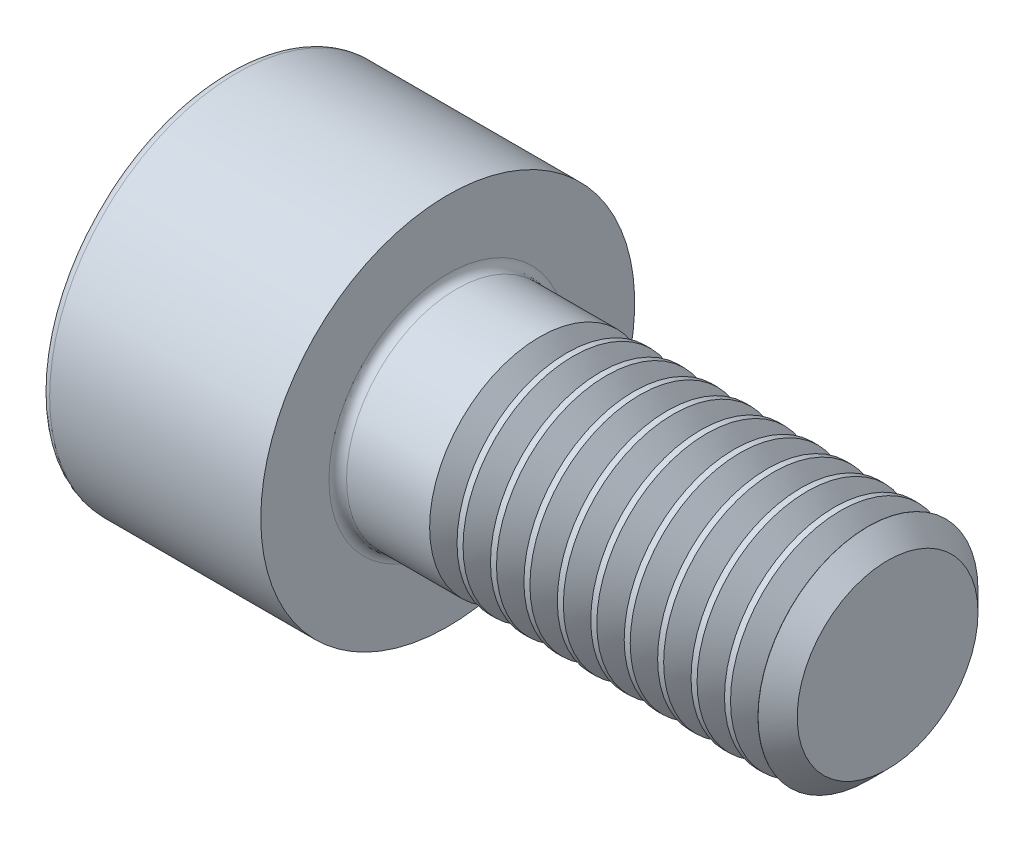
SolidWorks part; units mm, degrees
ref_plane "Front" through (0, 0, 0) normal (0, 0, 1) x (1, 0, 0)
ref_plane "Top" through (0, 0, 0) normal (0, 1, 0) x (1, 0, 0)
ref_plane "Right" through (0, 0, 0) normal (1, 0, 0) x (0, 0, -1)
ref_plane "Plane1" through (0, 0, 0) normal (0, 0, -1) x (-1, 0, 0)
sketch "Sketch1" plane through (0, 0, 0) normal (0, 0, -1) x (-1, 0, 0)
  line L0 (3.7906, 4.4808) -> (3.7906, 0.2308)
  line L1 (3.7906, 0.2308) -> (8.7906, 0.2308)
  line L2 (8.7906, 0.2308) -> (8.7906, 4.4808)
  line L3 (8.7906, 4.4808) -> (3.7906, 4.4808)
  line L4 (3.7906, 0.2308) -> (8.7906, 0.2308) construction
revolve "Revolve1" add sketch "Sketch1" angle 360 about L4
sketch "Sketch2" plane through (-3.7906, 0, 0) normal (1, 0, 0) x (0, 0, -1)
  circle A0 centre (0, 0.2308) radius 2.5
extrude "Boss-Extrude1" add sketch "Sketch2" along normal blind 2.0884
sketch "Sketch3" plane through (-1.7022, 0, 0) normal (1, 0, 0) x (0, 0, -1)
  circle A0 centre (0, 0.2308) radius 2.5
extrude "Boss-Extrude2" add sketch "Sketch3" along normal blind 0.3116 draft 55
sketch "Sketch4" plane through (-1.3906, 0, 0) normal (1, 0, 0) x (0, 0, -1)
  circle A0 centre (0, 0.2308) radius 2.055
extrude "Boss-Extrude3" add sketch "Sketch4" along normal blind 0.3116 draft 55 draft outward yes
sketch "Sketch5" plane through (-1.079, 0, 0) normal (1, 0, 0) x (0, 0, -1)
  circle A0 centre (0, 0.2308) radius 2.5
extrude "Boss-Extrude4" add sketch "Sketch5" along normal blind 0.1368
sketch "Sketch6" plane through (-0.9422, 0, 0) normal (1, 0, 0) x (0, 0, -1)
  circle A0 centre (0, 0.2308) radius 2.5
extrude "Boss-Extrude5" add sketch "Sketch6" along normal blind 0.3116 draft 55
sketch "Sketch7" plane through (-0.6306, 0, 0) normal (1, 0, 0) x (0, 0, -1)
  circle A0 centre (0, 0.2308) radius 2.055
extrude "Boss-Extrude6" add sketch "Sketch7" along normal blind 0.3116 draft 55 draft outward yes
sketch "Sketch8" plane through (-0.319, 0, 0) normal (1, 0, 0) x (0, 0, -1)
  circle A0 centre (0, 0.2308) radius 2.5
extrude "Boss-Extrude7" add sketch "Sketch8" along normal blind 0.1368
sketch "Sketch9" plane through (-0.1822, 0, 0) normal (1, 0, 0) x (0, 0, -1)
  circle A0 centre (0, 0.2308) radius 2.5
extrude "Boss-Extrude8" add sketch "Sketch9" along normal blind 0.3116 draft 55
sketch "Sketch10" plane through (0.1294, 0, 0) normal (1, 0, 0) x (0, 0, -1)
  circle A0 centre (0, 0.2308) radius 2.055
extrude "Boss-Extrude9" add sketch "Sketch10" along normal blind 0.3116 draft 55 draft outward yes
sketch "Sketch11" plane through (0.441, 0, 0) normal (1, 0, 0) x (0, 0, -1)
  circle A0 centre (0, 0.2308) radius 2.5
extrude "Boss-Extrude10" add sketch "Sketch11" along normal blind 0.1368
sketch "Sketch12" plane through (0.5778, 0, 0) normal (1, 0, 0) x (0, 0, -1)
  circle A0 centre (0, 0.2308) radius 2.5
extrude "Boss-Extrude11" add sketch "Sketch12" along normal blind 0.3116 draft 55
sketch "Sketch13" plane through (0.8894, 0, 0) normal (1, 0, 0) x (0, 0, -1)
  circle A0 centre (0, 0.2308) radius 2.055
extrude "Boss-Extrude12" add sketch "Sketch13" along normal blind 0.3116 draft 55 draft outward yes
sketch "Sketch14" plane through (1.201, 0, 0) normal (1, 0, 0) x (0, 0, -1)
  circle A0 centre (0, 0.2308) radius 2.5
extrude "Boss-Extrude13" add sketch "Sketch14" along normal blind 0.1368
sketch "Sketch15" plane through (1.3378, 0, 0) normal (1, 0, 0) x (0, 0, -1)
  circle A0 centre (0, 0.2308) radius 2.5
extrude "Boss-Extrude14" add sketch "Sketch15" along normal blind 0.3116 draft 55
sketch "Sketch16" plane through (1.6494, 0, 0) normal (1, 0, 0) x (0, 0, -1)
  circle A0 centre (0, 0.2308) radius 2.055
extrude "Boss-Extrude15" add sketch "Sketch16" along normal blind 0.3116 draft 55 draft outward yes
sketch "Sketch17" plane through (1.961, 0, 0) normal (1, 0, 0) x (0, 0, -1)
  circle A0 centre (0, 0.2308) radius 2.5
extrude "Boss-Extrude16" add sketch "Sketch17" along normal blind 0.1368
sketch "Sketch18" plane through (2.0978, 0, 0) normal (1, 0, 0) x (0, 0, -1)
  circle A0 centre (0, 0.2308) radius 2.5
extrude "Boss-Extrude17" add sketch "Sketch18" along normal blind 0.3116 draft 55
sketch "Sketch19" plane through (2.4094, 0, 0) normal (1, 0, 0) x (0, 0, -1)
  circle A0 centre (0, 0.2308) radius 2.055
extrude "Boss-Extrude18" add sketch "Sketch19" along normal blind 0.3116 draft 55 draft outward yes
sketch "Sketch20" plane through (2.721, 0, 0) normal (1, 0, 0) x (0, 0, -1)
  circle A0 centre (0, 0.2308) radius 2.5
extrude "Boss-Extrude19" add sketch "Sketch20" along normal blind 0.1368
sketch "Sketch21" plane through (2.8578, 0, 0) normal (1, 0, 0) x (0, 0, -1)
  circle A0 centre (0, 0.2308) radius 2.5
extrude "Boss-Extrude20" add sketch "Sketch21" along normal blind 0.3116 draft 55
sketch "Sketch22" plane through (3.1694, 0, 0) normal (1, 0, 0) x (0, 0, -1)
  circle A0 centre (0, 0.2308) radius 2.055
extrude "Boss-Extrude21" add sketch "Sketch22" along normal blind 0.3116 draft 55 draft outward yes
sketch "Sketch23" plane through (3.481, 0, 0) normal (1, 0, 0) x (0, 0, -1)
  circle A0 centre (0, 0.2308) radius 2.5
extrude "Boss-Extrude22" add sketch "Sketch23" along normal blind 0.1368
sketch "Sketch24" plane through (3.6178, 0, 0) normal (1, 0, 0) x (0, 0, -1)
  circle A0 centre (0, 0.2308) radius 2.5
extrude "Boss-Extrude23" add sketch "Sketch24" along normal blind 0.3116 draft 55
sketch "Sketch25" plane through (3.9294, 0, 0) normal (1, 0, 0) x (0, 0, -1)
  circle A0 centre (0, 0.2308) radius 2.055
extrude "Boss-Extrude24" add sketch "Sketch25" along normal blind 0.3116 draft 55 draft outward yes
sketch "Sketch26" plane through (4.241, 0, 0) normal (1, 0, 0) x (0, 0, -1)
  circle A0 centre (0, 0.2308) radius 2.5
extrude "Boss-Extrude25" add sketch "Sketch26" along normal blind 0.1368
sketch "Sketch27" plane through (4.3778, 0, 0) normal (1, 0, 0) x (0, 0, -1)
  circle A0 centre (0, 0.2308) radius 2.5
extrude "Boss-Extrude26" add sketch "Sketch27" along normal blind 0.3116 draft 55
sketch "Sketch28" plane through (4.6894, 0, 0) normal (1, 0, 0) x (0, 0, -1)
  circle A0 centre (0, 0.2308) radius 2.055
extrude "Boss-Extrude27" add sketch "Sketch28" along normal blind 0.3116 draft 55 draft outward yes
sketch "Sketch29" plane through (5.001, 0, 0) normal (1, 0, 0) x (0, 0, -1)
  circle A0 centre (0, 0.2308) radius 2.5
extrude "Boss-Extrude28" add sketch "Sketch29" along normal blind 0.1368
sketch "Sketch30" plane through (5.1378, 0, 0) normal (1, 0, 0) x (0, 0, -1)
  circle A0 centre (0, 0.2308) radius 2.5
extrude "Boss-Extrude29" add sketch "Sketch30" along normal blind 0.3116 draft 55
sketch "Sketch31" plane through (5.4494, 0, 0) normal (1, 0, 0) x (0, 0, -1)
  circle A0 centre (0, 0.2308) radius 2.055
extrude "Boss-Extrude30" add sketch "Sketch31" along normal blind 0.3116 draft 55 draft outward yes
sketch "Sketch32" plane through (5.761, 0, 0) normal (1, 0, 0) x (0, 0, -1)
  circle A0 centre (0, 0.2308) radius 2.5
extrude "Boss-Extrude31" add sketch "Sketch32" along normal blind 0.0034
sketch "Sketch33" plane through (5.7644, 0, 0) normal (1, 0, 0) x (0, 0, -1)
  circle A0 centre (0, 0.2308) radius 2.5
extrude "Boss-Extrude32" add sketch "Sketch33" along normal blind 0.445 draft 45
sketch "Sketch34" plane through (-8.7906, 0, 0) normal (-1, 0, 0) x (0, 0, 1)
  line L0 (0, -2.1271) -> (2.042, -0.9481)
  line L1 (2.042, -0.9481) -> (2.042, 1.4098)
  line L2 (2.042, 1.4098) -> (0, 2.5887)
  line L3 (0, 2.5887) -> (-2.042, 1.4098)
  line L4 (-2.042, 1.4098) -> (-2.042, -0.9481)
  line L5 (-2.042, -0.9481) -> (0, -2.1271)
extrude "Cut-Extrude1" cut sketch "Sketch34" against normal blind 2.5
sketch "Sketch35" plane through (0, 0, 0) normal (0, 0, 1) x (1, 0, 0)
  line L0 (-6.2906, 2.2728) -> (-6.2906, 0.2308)
  line L1 (-6.2906, 0.2308) -> (-5.1116, 0.2308)
  line L2 (-5.1116, 0.2308) -> (-6.2906, 2.2728)
  line L3 (-6.2906, 0.2308) -> (-5.1116, 0.2308) construction
revolve "Cut-Revolve1" cut sketch "Sketch35" angle 360 about L3
fillet "Fillet1" radius 0.2 2 edges at (-8.7906, 0.2308, 4.25) (-3.7906, 0.2308, -2.5)
